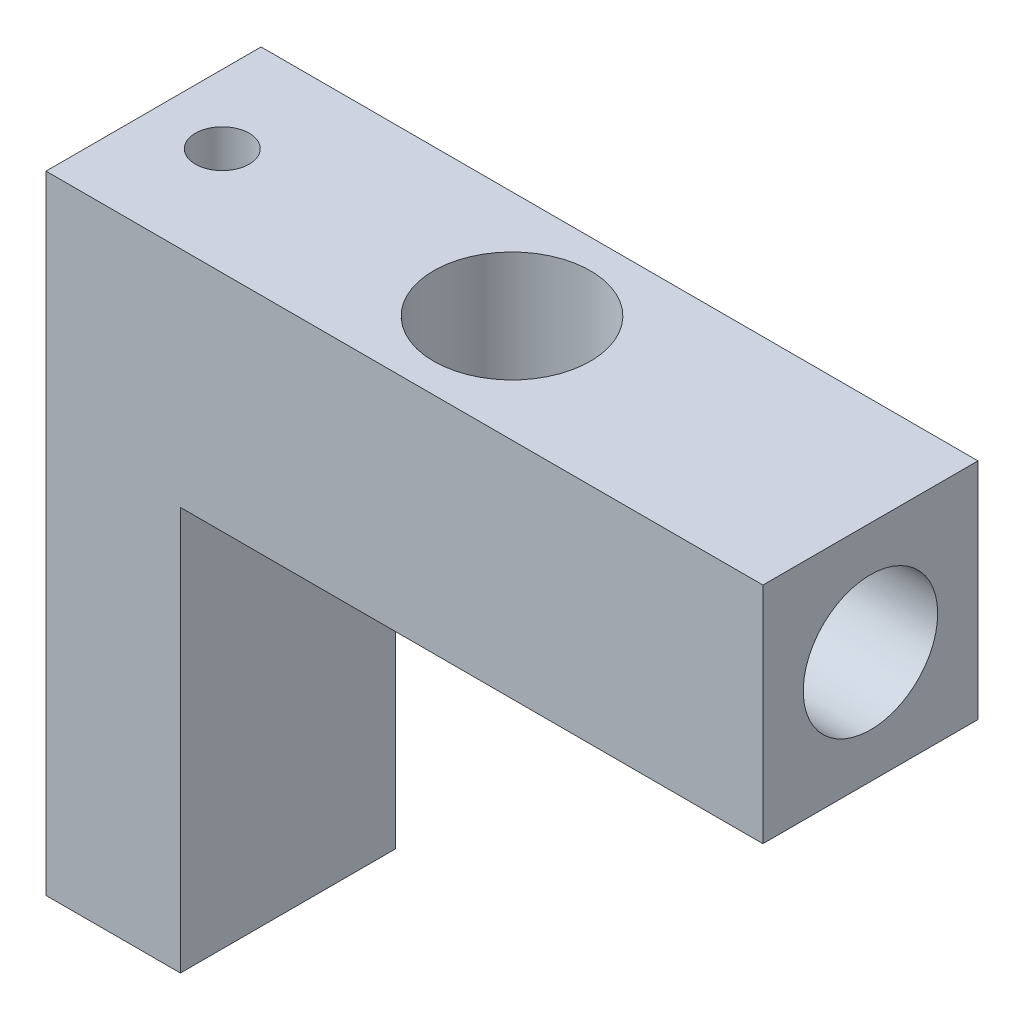
SolidWorks part; units mm, degrees
ref_plane "前视基准面" through (0, 0, 0) normal (0, 0, 1) x (1, 0, 0)
ref_plane "上视基准面" through (0, 0, 0) normal (0, 1, 0) x (1, 0, 0)
ref_plane "右视基准面" through (0, 0, 0) normal (1, 0, 0) x (0, 0, -1)
sketch "草图1" plane through (0, 0, 0) normal (0, 1, 0) x (1, 0, 0)
  line L1 (8, -2.4) -> (-8, -2.4)
  line L2 (8, -2.4) -> (8, 2.4)
  line L3 (8, 2.4) -> (-8, 2.4)
  line L4 (-8, -2.4) -> (-8, 2.4)
  line L5 (8, -2.4) -> (-8, 2.4) construction
  line L6 (8, 2.4) -> (-8, -2.4) construction
  circle A0 centre (0, 0) radius 1.75
  point P0 (0, 0)
  dimension "D1" = 3.5
  dimension "D2" = 4.8
  dimension "D3" = 16
extrude "凸台-拉伸1" add sketch "草图1" along normal blind 5
sketch "草图2" plane through (8, 0, 0) normal (1, 0, 0) x (0, 0, -1)
  line L0 (2.9359, 2.5) -> (-3.7197, 2.5) construction
  circle A0 centre (0, 2.5) radius 1.5
  dimension "D1" = 3
extrude "切除-拉伸1" cut sketch "草图2" against normal blind 3
sketch "草图3" plane through (5, 0, 0) normal (1, 0, 0) x (0, 0, -1)
  circle A0 centre (0, 2.5) radius 0.55
  dimension "D1" = 1.1
extrude "切除-拉伸2" cut sketch "草图3" against normal blind 4
sketch "草图5" plane through (0, 0, 0) normal (0, -1, 0) x (1, 0, 0)
  line L0 (8, -2.4) -> (-8, -2.4) construction
  line L1 (-8, 2.4) -> (-5, 2.4)
  line L2 (-8, 2.4) -> (-8, -2.4)
  line L3 (-8, -2.4) -> (-5, -2.4)
  line L4 (-5, 2.4) -> (-5, -2.4)
  dimension "D1" = 3
extrude "凸台-拉伸2" add sketch "草图5" along normal blind 9
sketch "草图6" plane through (0, -9, 0) normal (0, -1, 0) x (1, 0, 0)
  circle A0 centre (-6.4659, 0) radius 0.6
  dimension "D1" = 1.2
extrude "切除-拉伸3" cut sketch "草图6" against normal through all
